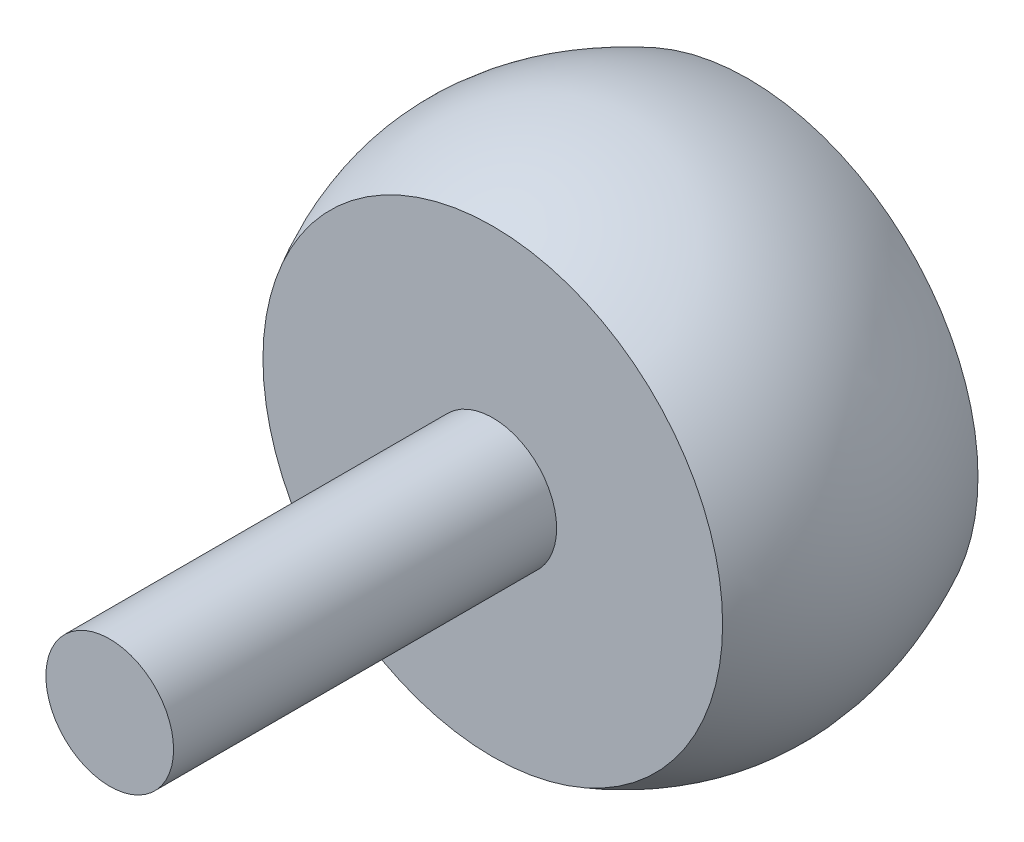
SolidWorks part; units mm, degrees
ref_plane "Front Plane" through (0, 0, 0) normal (0, 0, 1) x (1, 0, 0)
ref_plane "Top Plane" through (0, 0, 0) normal (0, 1, 0) x (1, 0, 0)
ref_plane "Right Plane" through (0, 0, 0) normal (1, 0, 0) x (0, 0, -1)
sketch "Sketch1" plane through (0, 0, 0) normal (0, 0, 1) x (1, 0, 0)
  circle A0 centre (0, 0) radius 9
  dimension "D1" = 18
extrude "Boss-Extrude1" add sketch "Sketch1" along normal blind 10
sketch "Sketch2" plane through (0, 0, 0) normal (1, 0, 0) x (0, 0, -1)
  line L1 (-17.8885, 0) -> (12.2661, 0) construction
  line L2 (-10, 9) -> (0, 9)
  spline S0 degree 3 poles (-10, 9) (-7.0253, 10.665) (-3.7509, 10.8777) (0, 9) knots 0 0 0 0 1 1 1 1
revolve "Revolve1" add sketch "Sketch2" angle 360 about L1
sketch "Sketch3" plane through (0, 0, 10) normal (0, 0, 1) x (1, 0, 0)
  circle A0 centre (0, 0) radius 2.5
  dimension "D1" = 5
extrude "Boss-Extrude2" add sketch "Sketch3" along normal blind 15
